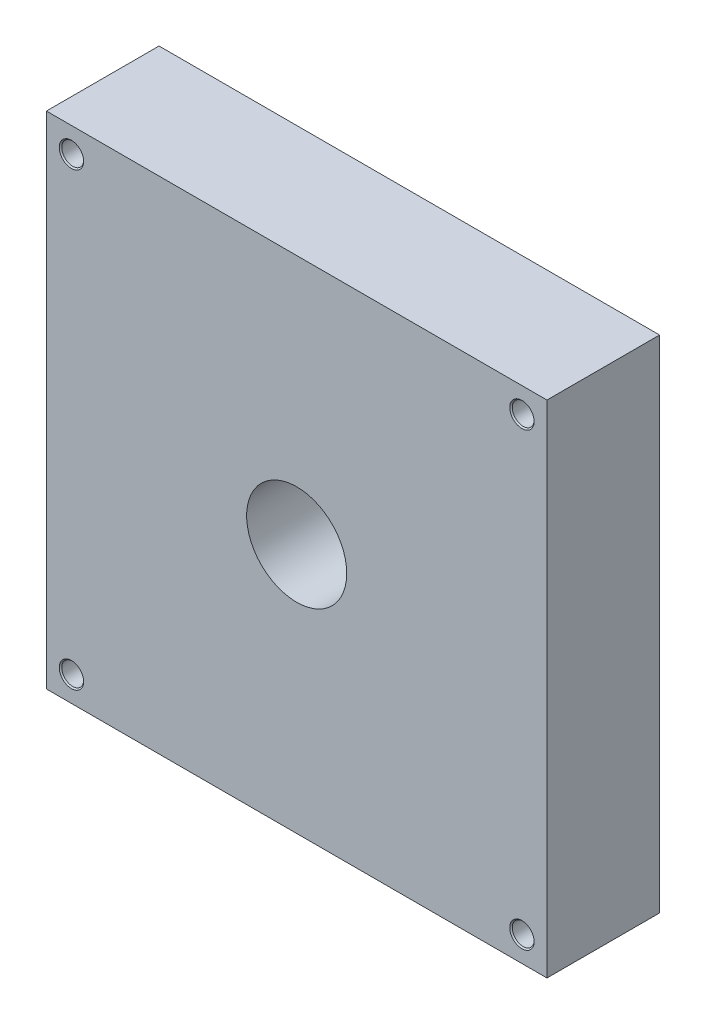
SolidWorks part; units mm, degrees
material "6061-T6 (SS)"
ref_plane "Front Plane" through (0, 0, 0) normal (0, 0, 1) x (1, 0, 0)
ref_plane "Top Plane" through (0, 0, 0) normal (0, 1, 0) x (1, 0, 0)
ref_plane "Right Plane" through (0, 0, 0) normal (1, 0, 0) x (0, 0, -1)
sketch "Sketch1" plane through (0, 0, 0) normal (0, 0, 1) x (1, 0, 0)
  line L1 (127, 127) -> (-127, 127)
  line L2 (127, 127) -> (127, -127)
  line L3 (127, -127) -> (-127, -127)
  line L4 (-127, 127) -> (-127, -127)
  line L5 (127, 127) -> (-127, -127) construction
  line L6 (127, -127) -> (-127, 127) construction
  line L7 (114.3, 114.3) -> (-114.3, 114.3) construction
  line L8 (114.3, 114.3) -> (114.3, -114.3) construction
  line L9 (114.3, -114.3) -> (-114.3, -114.3) construction
  line L10 (-114.3, 114.3) -> (-114.3, -114.3) construction
  line L11 (0, -114.3) -> (0, 114.3) construction
  line L12 (114.3, 0) -> (-114.3, 0) construction
  circle A0 centre (0, 0) radius 127
  circle A1 centre (0, 0) radius 25.4
  point P0 (0, 0)
  dimension "D3" = 50.8
  dimension "D1" = 254
  dimension "D2" = 228.6
extrude "Boss-Extrude1" add sketch "Sketch1" against normal blind 57.15 contours A0 L1 L4 | A0 A1 | A0 L4 L3 | A0 L3 L2 | A0 L2 L1
hole_wizard "CBORE for 1/4 Socket Head Cap Screw2" positions "Sketch2" profile "Sketch3" counterbore size "1/4" standard "ANSI Inch" end condition through all
sketch "Sketch2" plane through (0, 0, 0) normal (0, 0, 1) x (1, 0, 0)
  point P0 (-114.3, 114.3)
  point P3 (114.3, 114.3)
  point P6 (114.3, -114.3)
  point P9 (-114.3, -114.3)
sketch "Sketch3" plane through (-114.3, 114.3, 0) normal (1, 0, 0) x (0, -1, 0)
  line L0 (0, 0) -> (0, 57.15)
  line L1 (3.2639, 56.515) -> (3.8989, 57.15)
  line L2 (5.5562, 50.8) -> (3.2639, 50.8)
  line L3 (3.2639, 50.8) -> (3.2639, 56.515)
  line L5 (5.5562, 50.8) -> (5.5562, 0.635)
  line L6 (5.5562, 0.635) -> (6.1913, 0)
  line L7 (6.1913, 0) -> (0, 0)
  line L8 (-5.5562, 0.635) -> (-6.1913, 0) construction
  line L11 (0, -6.35) -> (0, 107.95) construction
  line L12 (3.8989, 57.15) -> (0, 57.15)
  line L13 (-3.2639, 56.515) -> (-3.8989, 57.15) construction
  dimension "Thru Hole Dia." = 6.5278
  dimension "Thru Hole Depth" = 57.15
  dimension "C'Bore Dia." = 11.1125
  dimension "C'Bore Depth" = 50.8
  dimension "Near C'Sink Dia." = 12.3825
  dimension "Near C'Sink Angle" = 90
  dimension "Far C'Sink Dia." = 7.7978
  dimension "Far C'Sink Angle" = 90
hole_wizard "#10-32 Tapped Hole1" positions "Sketch4" profile "Sketch6" tap size "#10-32" standard "ANSI Inch"
sketch "Sketch4" plane through (0, -127, 0) normal (0, -1, 0) x (-1, 0, 0)
  line L0 (0, 57.15) -> (0, 0) construction
  line L1 (-127, 57.15) -> (127, 57.15) construction
  line L3 (127, 57.15) -> (127, 0) construction
  line L4 (3.175, 25.4) -> (-9.525, 25.4) construction
  line L5 (37, 14.2875) -> (37, 36.5125) construction
  line L7 (-127, 0) -> (127, 0) construction
  line L8 (37, 25.4) -> (3.175, 25.4) construction
  point P0 (3.175, 25.4)
  point P12 (-9.525, 25.4)
  point P18 (37, 14.2875)
  point P20 (37, 36.5125)
  dimension "D1" = 123.825
  dimension "D2" = 12.7
  dimension "D3" = 90
  dimension "D5" = 25.4
  dimension "D6" = 22.225
sketch "Sketch6" plane through (-3.175, -127, -25.4) normal (1, 0, 0) x (0, 0, -1)
  line L0 (0, 0) -> (0, 20.2633)
  line L1 (0, 20.2633) -> (2.0193, 19.05)
  line L2 (2.0193, 19.05) -> (2.0193, 0)
  line L5 (2.0193, 0) -> (0, 0)
  line L10 (0, 20.2633) -> (-2.0193, 19.05) construction
  line L11 (0, -6.35) -> (0, 107.95) construction
  dimension "Tap Drill Dia." = 4.0386
  dimension "Tap Drill Depth" = 19.05
  dimension "Drill Angle" = 118
cosmetic thread "Hole Thread1" parameters "D1"=19.05, "D2"=4.826
cosmetic thread "Hole Thread2" parameters "D1"=19.05, "D2"=4.826
cosmetic thread "Hole Thread3" parameters "D1"=19.05, "D2"=4.826
cosmetic thread "Hole Thread4" parameters "D1"=19.05, "D2"=4.826
